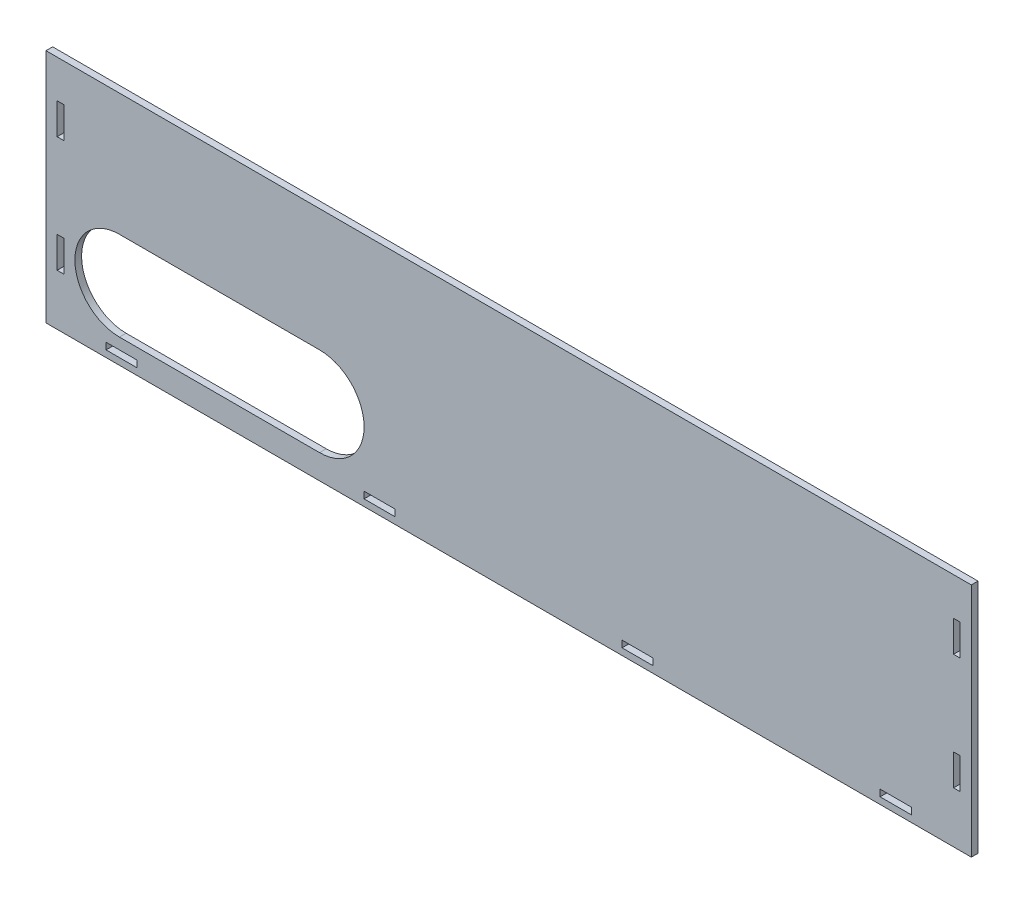
SolidWorks part; units mm, degrees
ref_plane "Front Plane" through (0, 0, 0) normal (0, 0, 1) x (1, 0, 0)
ref_plane "Top Plane" through (0, 0, 0) normal (0, 1, 0) x (1, 0, 0)
ref_plane "Right Plane" through (0, 0, 0) normal (1, 0, 0) x (0, 0, -1)
sketch "Sketch1" plane through (0, 0, 0) normal (0, 0, 1) x (1, 0, 0)
  line L1 (-208, -56) -> (208, -56)
  line L2 (-208, -56) -> (-208, 50)
  line L3 (-208, 50) -> (208, 50)
  line L4 (208, -56) -> (208, 50)
  point P0 (0, 0)
  dimension "D1" = 416
  dimension "D2" = 106
  dimension "D3" = 50
  dimension "D4" = 208
extrude "Boss-Extrude1" add sketch "Sketch1" along normal blind 3
sketch "Sketch2" plane through (0, 0, 3) normal (0, 0, 1) x (1, 0, 0)
  line L0 (0, 50) -> (0, -56) construction
  line L1 (208, 50) -> (-208, 50) construction
  line L2 (-208, -56) -> (208, -56) construction
  line L3 (203, 33) -> (203, 19)
  line L4 (-203, 33) -> (-200, 33)
  line L5 (-203, 33) -> (-203, 19)
  line L6 (-203, 19) -> (-200, 19)
  line L7 (-200, 33) -> (-200, 19)
  line L8 (203, 33) -> (200, 33)
  line L9 (200, 33) -> (200, 19)
  line L10 (203, 19) -> (200, 19)
  line L11 (203, -19) -> (203, -33)
  line L12 (-203, -19) -> (-200, -19)
  line L13 (-203, -19) -> (-203, -33)
  line L14 (-203, -33) -> (-200, -33)
  line L15 (-200, -19) -> (-200, -33)
  line L16 (203, -19) -> (200, -19)
  line L17 (200, -19) -> (200, -33)
  line L18 (203, -33) -> (200, -33)
  line L19 (181, -50) -> (181, -53)
  line L20 (-181, -50) -> (-167, -50)
  line L21 (-181, -50) -> (-181, -53)
  line L22 (-181, -53) -> (-167, -53)
  line L23 (-167, -50) -> (-167, -53)
  line L24 (181, -50) -> (167, -50)
  line L25 (167, -50) -> (167, -53)
  line L26 (181, -53) -> (167, -53)
  line L27 (65, -50) -> (65, -53)
  line L28 (-65, -50) -> (-51, -50)
  line L29 (-65, -50) -> (-65, -53)
  line L30 (-65, -53) -> (-51, -53)
  line L31 (-51, -50) -> (-51, -53)
  line L32 (65, -50) -> (51, -50)
  line L33 (51, -50) -> (51, -53)
  line L34 (65, -53) -> (51, -53)
  dimension "D1" = 14
  dimension "D2" = 3
  dimension "D3" = 14
  dimension "D4" = 3
  dimension "D5" = 200
  dimension "D6" = 19
  dimension "D7" = 19
  dimension "D8" = 200
  dimension "D9" = 14
  dimension "D10" = 3
  dimension "D11" = 50
  dimension "D12" = 51
  dimension "D13" = 14
  dimension "D14" = 3
  dimension "D15" = 167
  dimension "D16" = 50
extrude "Cut-Extrude1" cut sketch "Sketch2" against normal blind 3
sketch "Sketch4" plane through (0, 0, 3) normal (0, 0, 1) x (1, 0, 0)
  line L0 (-175, -25) -> (-85, -25) construction
  line L1 (-175, -5) -> (-85, -5)
  line L2 (-175, -45) -> (-85, -45)
  arc A0 (-175, -5) -> (-175, -45) centre (-175, -25) ccw
  arc A1 (-85, -45) -> (-85, -5) centre (-85, -25) ccw
  point P2 (-130, -25)
  dimension "D1" = 90
  dimension "D2" = 40
  dimension "D3" = 25
  dimension "D4" = 130
extrude "Cut-Extrude2" cut sketch "Sketch4" against normal blind 3
sketch "Sketch5" plane through (0, 0, 3) normal (0, 0, 1) x (1, 0, 0)
  text T0 "BOXY2" font "Century Gothic" height in points 22
  point P1 (-144, 0)
  dimension "D2" = 144
